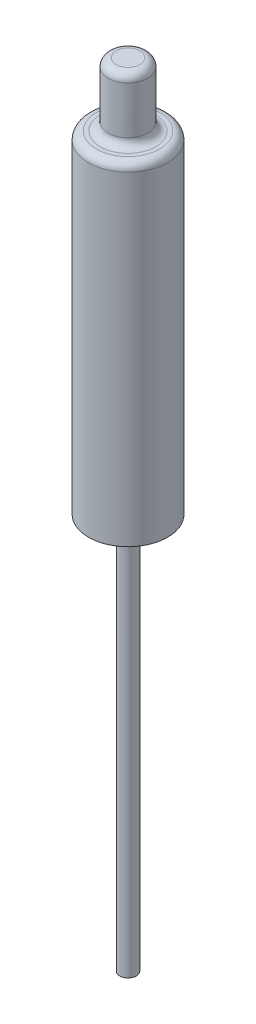
SolidWorks part; units mm, degrees
ref_plane "Plan de face" through (0, 0, 0) normal (0, 0, 1) x (1, 0, 0)
ref_plane "Plan de dessus" through (0, 0, 0) normal (0, 1, 0) x (1, 0, 0)
ref_plane "Plan de droite" through (0, 0, 0) normal (1, 0, 0) x (0, 0, -1)
sketch "Esquisse2" plane through (0, 0, 0) normal (0, 1, 0) x (1, 0, 0)
  circle A0 centre (0, 0) radius 1.05
  dimension "D1" = 2.1
extrude "Boss.-Extru.1" add sketch "Esquisse2" along normal blind 100
sketch "Esquisse3" plane through (0, 100, 0) normal (0, 1, 0) x (1, 0, 0)
  circle A0 centre (0, 0) radius 2.5
  dimension "D1" = 5
extrude "Boss.-Extru.2" add sketch "Esquisse3" against normal blind 8
sketch "Esquisse4" plane through (0, 92, 0) normal (0, -1, 0) x (1, 0, 0)
  circle A0 centre (0, 0) radius 5
  dimension "D1" = 10
extrude "Boss.-Extru.3" add sketch "Esquisse4" along normal blind 42
fillet "Congé4" radius 1 1 edges at (0, 100, 2.5)
fillet "Congé5" radius 1 1 edges at (0, 92, -5)
fillet "Congé6" radius 1 1 edges at (0, 92, -2.5)
